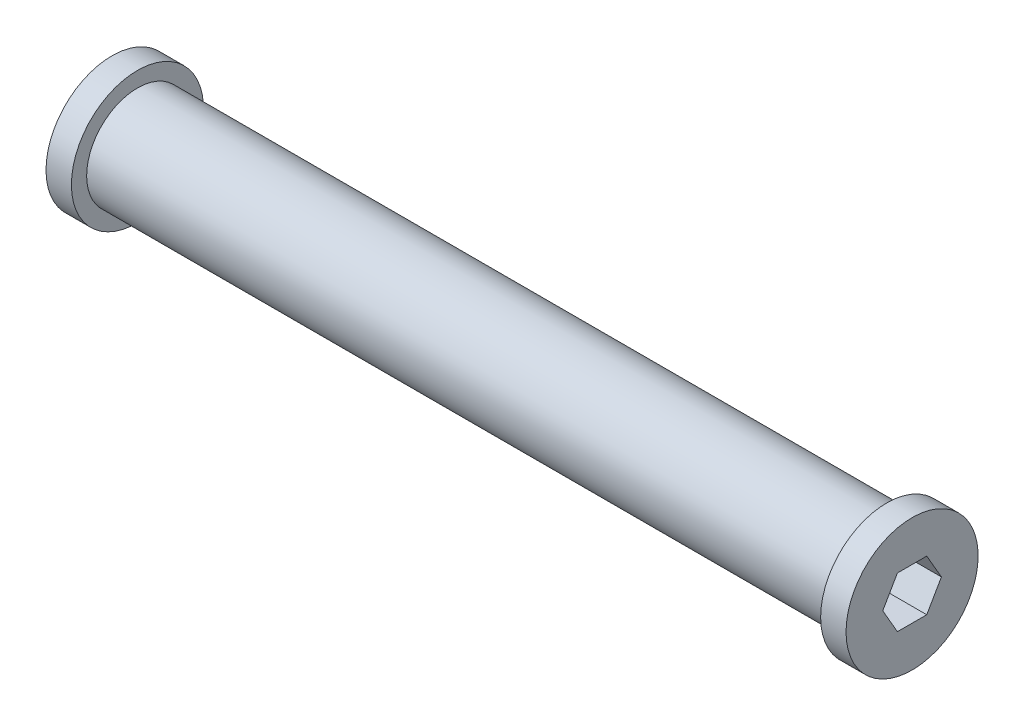
SolidWorks part; units mm, degrees
material "ABS"
ref_plane "Front Plane" through (0, 0, 0) normal (0, 0, 1) x (1, 0, 0)
ref_plane "Top Plane" through (0, 0, 0) normal (0, 1, 0) x (1, 0, 0)
ref_plane "Right Plane" through (0, 0, 0) normal (1, 0, 0) x (0, 0, -1)
sketch "Sketch1" plane through (0, 0, 0) normal (0, 0, 1) x (1, 0, 0)
  line L0 (0, 0) -> (58209.256, 0) construction
  line L1 (0, 0) -> (0, 6.35) construction
  line L2 (-100, 6.35) -> (100, 6.35)
  line L3 (100, 6.35) -> (100, 16.51)
  line L4 (100, 16.51) -> (93.65, 16.51)
  line L5 (93.65, 16.51) -> (93.65, 12.7)
  line L6 (93.65, 12.7) -> (-93.65, 12.7)
  line L7 (-93.65, 12.7) -> (-93.65, 16.51)
  line L8 (-93.65, 16.51) -> (-100, 16.51)
  line L9 (-100, 16.51) -> (-100, 6.35)
  circle A0 centre (-79.4209, 25.4) radius 10.5833 construction
  point P8 (0, 6.35)
  dimension "D5" = 21.1667
  dimension "D1" = 200
  dimension "D2" = 6.35
  dimension "D3" = 6.35
  dimension "D4" = 6.35
  dimension "D6" = 10.16
revolve "Revolve1" add sketch "Sketch1" angle 360 about L0
sketch "Sketch2" plane through (100, 0, 0) normal (1, 0, 0) x (0, 0, -1)
  line L1 (3.6662, 6.35) -> (-3.6662, 6.35)
  line L2 (-3.6662, 6.35) -> (-7.3323, 0)
  line L3 (-7.3323, 0) -> (-3.6662, -6.35)
  line L4 (-3.6662, -6.35) -> (3.6662, -6.35)
  line L5 (3.6662, -6.35) -> (7.3323, 0)
  line L6 (7.3323, 0) -> (3.6662, 6.35)
  circle A0 centre (0, 0) radius 6.35 construction
  circle A1 centre (0, 0) radius 6.35 construction
extrude "Cut-Extrude1" cut sketch "Sketch2" against normal through all
